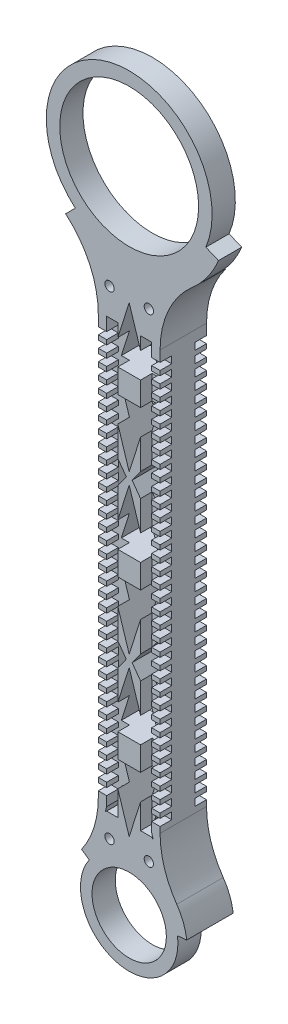
SolidWorks part; units mm, degrees
ref_plane "Front Plane" through (0, 0, 0) normal (0, 0, 1) x (1, 0, 0)
ref_plane "Top Plane" through (0, 0, 0) normal (0, 1, 0) x (1, 0, 0)
ref_plane "Right Plane" through (0, 0, 0) normal (1, 0, 0) x (0, 0, -1)
sketch "Sketch1" plane through (0, 0, 0) normal (0, 0, 1) x (1, 0, 0)
  line L0 (41.9129, -70.1056) -> (48.8352, -72.9599)
  line L1 (-29.4421, -87.2986) -> (-34.7507, -92.6073)
  line L6 (-16.891, -360.115) -> (-16.891, -131.2827)
  line L8 (16.891, -360.115) -> (16.891, -131.2827)
  circle A0 centre (0, -52.8237) radius 37.9584
  arc A1 (41.9129, -70.1056) -> (-29.4421, -87.2986) centre (0, -52.8237) ccw
  arc A2 (-34.7507, -92.6073) -> (-34.5065, -92.8193) centre (0, -52.8237) ccw
  arc A3 (34.5065, -92.8193) -> (48.8352, -72.9599) centre (0, -52.8237) ccw
  arc A4 (16.891, -131.2827) -> (34.5065, -92.8193) centre (67.691, -131.2827) cw
  arc A5 (-16.891, -131.2827) -> (-34.5065, -92.8193) centre (-67.691, -131.2827) ccw
  arc A6 (-26.0165, -389.1645) -> (26.0165, -389.1645) centre (0, -407.2996) ccw
  arc A7 (16.891, -360.115) -> (26.0165, -389.1645) centre (67.691, -360.115) ccw
  arc A8 (-16.891, -360.115) -> (-26.0165, -389.1645) centre (-67.691, -360.115) cw
  point P3 (0, -307.0431)
  dimension "D1" = 50.8
  dimension "D2" = 50.8
extrude "Boss-Extrude1" add sketch "Sketch1" along normal blind 12.7
sketch "Sketch2" plane through (0, 0, 12.7) normal (0, 0, 1) x (1, 0, 0)
  circle A0 centre (0, -407.2996) radius 20.32
  dimension "D1" = 40.64
extrude "Cut-Extrude1" cut sketch "Sketch2" against normal through all
sketch "Sketch3" plane through (0, 0, 12.7) normal (0, 0, 1) x (1, 0, 0)
  line L0 (31.4667, -403.3512) -> (26.4093, -403.8521)
  line L2 (-21.8491, -392.0695) -> (-26.0165, -389.1645)
  arc A2 (-26.0165, -389.1645) -> (26.0165, -389.1645) centre (0, -407.2996) ccw construction
  arc A5 (-26.0165, -389.1645) -> (31.4667, -403.3512) centre (0, -407.2996) ccw
  arc A7 (-21.8491, -392.0695) -> (26.4093, -403.8521) centre (0, -407.2996) ccw
  arc A9 (-21.8491, -392.0695) -> (21.8491, -392.0695) centre (0, -407.2996) ccw construction
  arc A10 (-26.0165, -389.1645) -> (26.0165, -389.1645) centre (0, -407.2996) ccw construction
  arc A11 (16.891, -360.115) -> (26.0165, -389.1645) centre (67.691, -360.115) ccw construction
  arc A12 (11.811, -360.115) -> (21.8491, -392.0695) centre (67.691, -360.115) ccw construction
  arc A13 (-21.8491, -392.0695) -> (-11.811, -360.115) centre (-67.691, -360.115) ccw construction
  arc A14 (-26.0165, -389.1645) -> (-16.891, -360.115) centre (-67.691, -360.115) ccw construction
  dimension "D1" = 5.08
extrude "Cut-Extrude2" cut sketch "Sketch3" against normal through all
sketch "Sketch4" plane through (0, 0, 0) normal (0, 0, -1) x (-1, 0, 0)
  line L0 (-31.4667, -403.3512) -> (-26.4093, -403.8521) construction
  line L1 (21.8491, -392.0695) -> (26.0165, -389.1645) construction
  line L2 (-16.891, -360.115) -> (-16.891, -131.2827) construction
  line L3 (16.891, -131.2827) -> (16.891, -360.115) construction
  line L4 (-31.4667, -403.3512) -> (-27.7291, -403.7214)
  line L5 (22.9366, -391.3114) -> (26.0165, -389.1645)
  line L6 (-16.891, -360.115) -> (-16.891, -131.2827)
  line L7 (16.891, -131.2827) -> (16.891, -360.115)
  arc A0 (-27.4428, -100.2871) -> (27.4428, -100.2871) centre (0, -52.8237) ccw
  arc A1 (22.9366, -391.3114) -> (-27.7291, -403.7214) centre (0, -407.2996) ccw
  arc A2 (-26.0165, -389.1645) -> (-31.4667, -403.3512) centre (0, -407.2996) ccw construction
  arc A3 (-26.0165, -389.1645) -> (-16.891, -360.115) centre (-67.691, -360.115) ccw construction
  arc A4 (16.891, -360.115) -> (26.0165, -389.1645) centre (67.691, -360.115) ccw construction
  arc A5 (-16.891, -131.2827) -> (-34.5065, -92.8193) centre (-67.691, -131.2827) ccw construction
  arc A6 (34.5065, -92.8193) -> (16.891, -131.2827) centre (67.691, -131.2827) ccw construction
  arc A7 (-26.0165, -389.1645) -> (-31.4667, -403.3512) centre (0, -407.2996) ccw
  arc A8 (-26.0165, -389.1645) -> (-16.891, -360.115) centre (-67.691, -360.115) ccw
  arc A9 (16.891, -360.115) -> (26.0165, -389.1645) centre (67.691, -360.115) ccw
  arc A10 (-16.891, -131.2827) -> (-27.4428, -100.2871) centre (-67.691, -131.2827) ccw
  arc A11 (27.4428, -100.2871) -> (16.891, -131.2827) centre (67.691, -131.2827) ccw
extrude "Boss-Extrude2" add sketch "Sketch4" along normal blind 12.7
sketch "Sketch5" plane through (0, 0, -12.7) normal (0, 0, -1) x (-1, 0, 0)
  line L0 (0, -52.8237) -> (0, -407.2996) construction
  line L1 (0, -117.3287) -> (-10.643, -150.8506)
  line L2 (-10.643, -150.8506) -> (10.643, -150.8506)
  line L3 (0, -117.3287) -> (10.643, -150.8506)
  line L4 (-13.7523, -157.3804) -> (13.3679, -157.3804) construction
  line L5 (-10.643, -163.9102) -> (10.643, -163.9102)
  line L6 (0, -197.4321) -> (-10.643, -163.9102)
  line L7 (0, -197.4321) -> (10.643, -163.9102)
  line L8 (0, -203.6887) -> (-10.643, -237.2106)
  line L9 (0, -203.6887) -> (10.643, -237.2106)
  line L10 (-10.643, -237.2106) -> (10.643, -237.2106)
  line L11 (-10.643, -250.2702) -> (10.643, -250.2702)
  line L12 (0, -283.7921) -> (-10.643, -250.2702)
  line L13 (0, -283.7921) -> (10.643, -250.2702)
  line L14 (0, -290.0487) -> (-10.643, -323.5706)
  line L15 (0, -290.0487) -> (10.643, -323.5706)
  line L16 (-10.643, -323.5706) -> (10.643, -323.5706)
  line L17 (-10.643, -336.6302) -> (10.643, -336.6302)
  line L18 (0, -370.1521) -> (-10.643, -336.6302)
  line L19 (0, -370.1521) -> (10.643, -336.6302)
  point P9 (0, -150.8506)
  dimension "D1" = 3
extrude "Cut-Extrude3" cut sketch "Sketch5" against normal through all
sketch "Sketch6" plane through (0, 0, -12.7) normal (0, 0, -1) x (-1, 0, 0)
  line L0 (0, -237.2106) -> (0, -250.2702) construction
  line L1 (-10.643, -237.2106) -> (10.643, -237.2106) construction
  line L2 (10.643, -250.2702) -> (-10.643, -250.2702) construction
  line L3 (0, -243.7404) -> (-16.891, -243.7404) construction
  line L4 (-16.891, -131.2827) -> (-16.891, -360.115) construction
  line L5 (0, -197.4321) -> (0, -203.6887) construction
  line L6 (-1.5941, -200.5506) -> (-16.891, -200.5506) construction
  line L7 (-1.5941, -200.5506) -> (-14.024, -183.3482)
  line L8 (-14.024, -183.3482) -> (-14.024, -217.753)
  line L9 (-1.5941, -200.5506) -> (-14.024, -217.753)
  line L10 (1.5941, -200.5506) -> (14.024, -217.753)
  line L11 (14.024, -183.3482) -> (14.024, -217.753)
  line L12 (1.5941, -200.5506) -> (14.024, -183.3482)
  line L13 (14.024, -304.1326) -> (14.024, -269.7279)
  line L14 (1.5941, -286.9302) -> (14.024, -269.7279)
  line L15 (-1.5941, -286.9302) -> (-14.024, -269.7279)
  line L16 (-14.024, -304.1326) -> (-14.024, -269.7279)
  line L17 (-1.5941, -286.9302) -> (-14.024, -304.1326)
  line L18 (1.5941, -286.9302) -> (14.024, -304.1326)
  line L25 (-10.1561, -354.1919) -> (-7.6855, -361.1596)
  line L26 (-13.0919, -364.9672) -> (-10.1561, -354.1919)
  line L28 (13.0919, -364.9672) -> (10.1561, -354.1919)
  line L29 (10.1561, -354.1919) -> (7.6855, -361.1596)
  arc A0 (13.0919, -364.9672) -> (7.6855, -361.1596) centre (0, -377.8143) ccw
  arc A1 (-7.6855, -361.1596) -> (-13.0919, -364.9672) centre (0, -377.8143) ccw
  point P19 (-14.024, -200.5506)
extrude "Cut-Extrude4" cut sketch "Sketch6" against normal through all
sketch "Sketch7" plane through (0, 0, -12.7) normal (0, 0, -1) x (-1, 0, 0)
  line L0 (-14.9497, -173.4575) -> (-14.9497, -317.6758)
  line L1 (-14.9497, -317.6758) -> (-12.2901, -317.6758)
  line L2 (0, -237.2106) -> (0, -250.2702) construction
  line L3 (-14.9497, -173.4575) -> (-12.2901, -173.4575)
  line L4 (-12.2901, -317.6758) -> (-12.2901, -173.4575)
  line L5 (-14.9497, -245.5666) -> (-12.2901, -173.4575) construction
  line L6 (-14.9497, -245.5666) -> (-12.2901, -317.6758) construction
  line L7 (-10.643, -237.2106) -> (10.643, -237.2106) construction
  line L8 (10.643, -250.2702) -> (-10.643, -250.2702) construction
  line L9 (14.9497, -317.6758) -> (12.2901, -317.6758)
  line L10 (14.9497, -173.4575) -> (12.2901, -173.4575)
  line L11 (14.9497, -173.4575) -> (14.9497, -317.6758)
  line L12 (12.2901, -317.6758) -> (12.2901, -173.4575)
  point P0 (-14.9497, -245.5666)
extrude "Boss-Extrude3" add sketch "Sketch7" against normal up to surface (25.4 mm away) up to face at (-9.8807, -286.9302, 12.7)
sketch "Sketch8" plane through (0, 0, -12.7) normal (0, 0, -1) x (-1, 0, 0)
  line L0 (0, -117.3287) -> (0, -174.7618) construction
  line L1 (16.891, -245.6988) -> (-16.891, -245.6988) construction
  line L2 (16.891, -360.115) -> (16.891, -131.2827) construction
  line L3 (-16.891, -131.2827) -> (-16.891, -360.115) construction
  circle A0 centre (-10.7564, -114.872) radius 2.54
  circle A1 centre (10.7564, -114.872) radius 2.54
  circle A2 centre (-10.7564, -376.5256) radius 2.54
  circle A3 centre (10.7564, -376.5256) radius 2.54
  dimension "D1" = 5.08
extrude "Cut-Extrude5" cut sketch "Sketch8" against normal through all
sketch "Sketch9" plane through (16.891, 0, 0) normal (1, 0, 0) x (0, 0, -1)
  line L0 (12.7, -131.2827) -> (12.7, -360.115) construction
  line L1 (12.7, -353.0709) -> (6.35, -353.0709)
  line L2 (12.7, -346.7209) -> (6.35, -346.7209)
  line L3 (12.7, -356.8809) -> (6.35, -356.8809)
  line L4 (6.35, -353.0709) -> (6.35, -356.8809)
  line L5 (12.7, -354.9759) -> (6.35, -356.8809) construction
  line L6 (12.7, -354.9759) -> (6.35, -353.0709) construction
  line L7 (12.7, -353.0709) -> (12.7, -356.8809)
  line L8 (12.7, -346.7209) -> (12.7, -350.5309)
  line L9 (6.35, -346.7209) -> (6.35, -350.5309)
  line L10 (12.7, -350.5309) -> (6.35, -350.5309)
  line L11 (12.7, -340.3709) -> (6.35, -340.3709)
  line L12 (12.7, -340.3709) -> (12.7, -344.1809)
  line L13 (6.35, -340.3709) -> (6.35, -344.1809)
  line L14 (12.7, -344.1809) -> (6.35, -344.1809)
  line L15 (12.7, -334.0209) -> (6.35, -334.0209)
  line L16 (12.7, -334.0209) -> (12.7, -337.8309)
  line L17 (6.35, -334.0209) -> (6.35, -337.8309)
  line L18 (12.7, -337.8309) -> (6.35, -337.8309)
  line L19 (12.7, -327.6709) -> (6.35, -327.6709)
  line L20 (12.7, -327.6709) -> (12.7, -331.4809)
  line L21 (6.35, -327.6709) -> (6.35, -331.4809)
  line L22 (12.7, -331.4809) -> (6.35, -331.4809)
  line L23 (12.7, -321.3209) -> (6.35, -321.3209)
  line L24 (12.7, -321.3209) -> (12.7, -325.1309)
  line L25 (6.35, -321.3209) -> (6.35, -325.1309)
  line L26 (12.7, -325.1309) -> (6.35, -325.1309)
  line L27 (12.7, -314.9709) -> (6.35, -314.9709)
  line L28 (12.7, -314.9709) -> (12.7, -318.7809)
  line L29 (6.35, -314.9709) -> (6.35, -318.7809)
  line L30 (12.7, -318.7809) -> (6.35, -318.7809)
  line L31 (12.7, -308.6209) -> (6.35, -308.6209)
  line L32 (12.7, -308.6209) -> (12.7, -312.4309)
  line L33 (6.35, -308.6209) -> (6.35, -312.4309)
  line L34 (12.7, -312.4309) -> (6.35, -312.4309)
  line L35 (12.7, -302.2709) -> (6.35, -302.2709)
  line L36 (12.7, -302.2709) -> (12.7, -306.0809)
  line L37 (6.35, -302.2709) -> (6.35, -306.0809)
  line L38 (12.7, -306.0809) -> (6.35, -306.0809)
  line L39 (12.7, -295.9209) -> (6.35, -295.9209)
  line L40 (12.7, -295.9209) -> (12.7, -299.7309)
  line L41 (6.35, -295.9209) -> (6.35, -299.7309)
  line L42 (12.7, -299.7309) -> (6.35, -299.7309)
  line L43 (12.7, -289.5709) -> (6.35, -289.5709)
  line L44 (12.7, -289.5709) -> (12.7, -293.3809)
  line L45 (6.35, -289.5709) -> (6.35, -293.3809)
  line L46 (12.7, -293.3809) -> (6.35, -293.3809)
  line L47 (12.7, -283.2209) -> (6.35, -283.2209)
  line L48 (12.7, -283.2209) -> (12.7, -287.0309)
  line L49 (6.35, -283.2209) -> (6.35, -287.0309)
  line L50 (12.7, -287.0309) -> (6.35, -287.0309)
  line L51 (12.7, -276.8709) -> (6.35, -276.8709)
  line L52 (12.7, -276.8709) -> (12.7, -280.6809)
  line L53 (6.35, -276.8709) -> (6.35, -280.6809)
  line L54 (12.7, -280.6809) -> (6.35, -280.6809)
  line L55 (12.7, -270.5209) -> (6.35, -270.5209)
  line L56 (12.7, -270.5209) -> (12.7, -274.3309)
  line L57 (6.35, -270.5209) -> (6.35, -274.3309)
  line L58 (12.7, -274.3309) -> (6.35, -274.3309)
  line L59 (12.7, -264.1709) -> (6.35, -264.1709)
  line L60 (12.7, -264.1709) -> (12.7, -267.9809)
  line L61 (6.35, -264.1709) -> (6.35, -267.9809)
  line L62 (12.7, -267.9809) -> (6.35, -267.9809)
  line L63 (12.7, -257.8209) -> (6.35, -257.8209)
  line L64 (12.7, -257.8209) -> (12.7, -261.6309)
  line L65 (6.35, -257.8209) -> (6.35, -261.6309)
  line L66 (12.7, -261.6309) -> (6.35, -261.6309)
  line L67 (12.7, -251.4709) -> (6.35, -251.4709)
  line L68 (12.7, -251.4709) -> (12.7, -255.2809)
  line L69 (6.35, -251.4709) -> (6.35, -255.2809)
  line L70 (12.7, -255.2809) -> (6.35, -255.2809)
  line L71 (12.7, -245.1209) -> (6.35, -245.1209)
  line L72 (12.7, -245.1209) -> (12.7, -248.9309)
  line L73 (6.35, -245.1209) -> (6.35, -248.9309)
  line L74 (12.7, -248.9309) -> (6.35, -248.9309)
  line L75 (12.7, -238.7709) -> (6.35, -238.7709)
  line L76 (12.7, -238.7709) -> (12.7, -242.5809)
  line L77 (6.35, -238.7709) -> (6.35, -242.5809)
  line L78 (12.7, -242.5809) -> (6.35, -242.5809)
  line L79 (12.7, -232.4209) -> (6.35, -232.4209)
  line L80 (12.7, -232.4209) -> (12.7, -236.2309)
  line L81 (6.35, -232.4209) -> (6.35, -236.2309)
  line L82 (12.7, -236.2309) -> (6.35, -236.2309)
  line L83 (12.7, -226.0709) -> (6.35, -226.0709)
  line L84 (12.7, -226.0709) -> (12.7, -229.8809)
  line L85 (6.35, -226.0709) -> (6.35, -229.8809)
  line L86 (12.7, -229.8809) -> (6.35, -229.8809)
  line L87 (12.7, -219.7209) -> (6.35, -219.7209)
  line L88 (12.7, -219.7209) -> (12.7, -223.5309)
  line L89 (6.35, -219.7209) -> (6.35, -223.5309)
  line L90 (12.7, -223.5309) -> (6.35, -223.5309)
  line L91 (12.7, -213.3709) -> (6.35, -213.3709)
  line L92 (12.7, -213.3709) -> (12.7, -217.1809)
  line L93 (6.35, -213.3709) -> (6.35, -217.1809)
  line L94 (12.7, -217.1809) -> (6.35, -217.1809)
  line L95 (12.7, -207.0209) -> (6.35, -207.0209)
  line L96 (12.7, -207.0209) -> (12.7, -210.8309)
  line L97 (6.35, -207.0209) -> (6.35, -210.8309)
  line L98 (12.7, -210.8309) -> (6.35, -210.8309)
  line L99 (12.7, -200.6709) -> (6.35, -200.6709)
  line L100 (12.7, -200.6709) -> (12.7, -204.4809)
  line L101 (6.35, -200.6709) -> (6.35, -204.4809)
  line L102 (12.7, -204.4809) -> (6.35, -204.4809)
  line L103 (12.7, -194.3209) -> (6.35, -194.3209)
  line L104 (12.7, -194.3209) -> (12.7, -198.1309)
  line L105 (6.35, -194.3209) -> (6.35, -198.1309)
  line L106 (12.7, -198.1309) -> (6.35, -198.1309)
  line L107 (12.7, -187.9709) -> (6.35, -187.9709)
  line L108 (12.7, -187.9709) -> (12.7, -191.7809)
  line L109 (6.35, -187.9709) -> (6.35, -191.7809)
  line L110 (12.7, -191.7809) -> (6.35, -191.7809)
  line L111 (12.7, -181.6209) -> (6.35, -181.6209)
  line L112 (12.7, -181.6209) -> (12.7, -185.4309)
  line L113 (6.35, -181.6209) -> (6.35, -185.4309)
  line L114 (12.7, -185.4309) -> (6.35, -185.4309)
  line L115 (12.7, -175.2709) -> (6.35, -175.2709)
  line L116 (12.7, -175.2709) -> (12.7, -179.0809)
  line L117 (6.35, -175.2709) -> (6.35, -179.0809)
  line L118 (12.7, -179.0809) -> (6.35, -179.0809)
  line L119 (12.7, -168.9209) -> (6.35, -168.9209)
  line L120 (12.7, -168.9209) -> (12.7, -172.7309)
  line L121 (6.35, -168.9209) -> (6.35, -172.7309)
  line L122 (12.7, -172.7309) -> (6.35, -172.7309)
  line L123 (12.7, -162.5709) -> (6.35, -162.5709)
  line L124 (12.7, -162.5709) -> (12.7, -166.3809)
  line L125 (6.35, -162.5709) -> (6.35, -166.3809)
  line L126 (12.7, -166.3809) -> (6.35, -166.3809)
  line L127 (12.7, -156.2209) -> (6.35, -156.2209)
  line L128 (12.7, -156.2209) -> (12.7, -160.0309)
  line L129 (6.35, -156.2209) -> (6.35, -160.0309)
  line L130 (12.7, -160.0309) -> (6.35, -160.0309)
  line L131 (12.7, -149.8709) -> (6.35, -149.8709)
  line L132 (12.7, -149.8709) -> (12.7, -153.6809)
  line L133 (6.35, -149.8709) -> (6.35, -153.6809)
  line L134 (12.7, -153.6809) -> (6.35, -153.6809)
  line L135 (12.7, -143.5209) -> (6.35, -143.5209)
  line L136 (12.7, -143.5209) -> (12.7, -147.3309)
  line L137 (6.35, -143.5209) -> (6.35, -147.3309)
  line L138 (12.7, -147.3309) -> (6.35, -147.3309)
  line L139 (12.7, -137.1709) -> (6.35, -137.1709)
  line L140 (12.7, -137.1709) -> (12.7, -140.9809)
  line L141 (6.35, -137.1709) -> (6.35, -140.9809)
  line L142 (12.7, -140.9809) -> (6.35, -140.9809)
  line L143 (0, -131.2827) -> (0, -360.115) construction
  line L144 (-12.7, -131.2827) -> (12.7, -131.2827) construction
  line L145 (-12.7, -360.115) -> (12.7, -360.115) construction
  line L146 (-12.7, -354.9759) -> (-6.35, -353.0709) construction
  line L147 (-12.7, -354.9759) -> (-6.35, -356.8809) construction
  line L148 (-12.7, -140.9809) -> (-6.35, -140.9809)
  line L149 (-6.35, -137.1709) -> (-6.35, -140.9809)
  line L150 (-12.7, -137.1709) -> (-12.7, -140.9809)
  line L151 (-12.7, -137.1709) -> (-6.35, -137.1709)
  line L152 (-12.7, -147.3309) -> (-6.35, -147.3309)
  line L153 (-6.35, -143.5209) -> (-6.35, -147.3309)
  line L154 (-12.7, -143.5209) -> (-12.7, -147.3309)
  line L155 (-12.7, -143.5209) -> (-6.35, -143.5209)
  line L156 (-12.7, -153.6809) -> (-6.35, -153.6809)
  line L157 (-6.35, -149.8709) -> (-6.35, -153.6809)
  line L158 (-12.7, -149.8709) -> (-12.7, -153.6809)
  line L159 (-12.7, -149.8709) -> (-6.35, -149.8709)
  line L160 (-12.7, -160.0309) -> (-6.35, -160.0309)
  line L161 (-6.35, -156.2209) -> (-6.35, -160.0309)
  line L162 (-12.7, -156.2209) -> (-12.7, -160.0309)
  line L163 (-12.7, -156.2209) -> (-6.35, -156.2209)
  line L164 (-12.7, -166.3809) -> (-6.35, -166.3809)
  line L165 (-6.35, -162.5709) -> (-6.35, -166.3809)
  line L166 (-12.7, -162.5709) -> (-12.7, -166.3809)
  line L167 (-12.7, -162.5709) -> (-6.35, -162.5709)
  line L168 (-12.7, -172.7309) -> (-6.35, -172.7309)
  line L169 (-6.35, -168.9209) -> (-6.35, -172.7309)
  line L170 (-12.7, -168.9209) -> (-12.7, -172.7309)
  line L171 (-12.7, -168.9209) -> (-6.35, -168.9209)
  line L172 (-12.7, -179.0809) -> (-6.35, -179.0809)
  line L173 (-6.35, -175.2709) -> (-6.35, -179.0809)
  line L174 (-12.7, -175.2709) -> (-12.7, -179.0809)
  line L175 (-12.7, -175.2709) -> (-6.35, -175.2709)
  line L176 (-12.7, -185.4309) -> (-6.35, -185.4309)
  line L177 (-6.35, -181.6209) -> (-6.35, -185.4309)
  line L178 (-12.7, -181.6209) -> (-12.7, -185.4309)
  line L179 (-12.7, -181.6209) -> (-6.35, -181.6209)
  line L180 (-12.7, -191.7809) -> (-6.35, -191.7809)
  line L181 (-6.35, -187.9709) -> (-6.35, -191.7809)
  line L182 (-12.7, -187.9709) -> (-12.7, -191.7809)
  line L183 (-12.7, -187.9709) -> (-6.35, -187.9709)
  line L184 (-12.7, -198.1309) -> (-6.35, -198.1309)
  line L185 (-6.35, -194.3209) -> (-6.35, -198.1309)
  line L186 (-12.7, -194.3209) -> (-12.7, -198.1309)
  line L187 (-12.7, -194.3209) -> (-6.35, -194.3209)
  line L188 (-12.7, -204.4809) -> (-6.35, -204.4809)
  line L189 (-6.35, -200.6709) -> (-6.35, -204.4809)
  line L190 (-12.7, -200.6709) -> (-12.7, -204.4809)
  line L191 (-12.7, -200.6709) -> (-6.35, -200.6709)
  line L192 (-12.7, -210.8309) -> (-6.35, -210.8309)
  line L193 (-6.35, -207.0209) -> (-6.35, -210.8309)
  line L194 (-12.7, -207.0209) -> (-12.7, -210.8309)
  line L195 (-12.7, -207.0209) -> (-6.35, -207.0209)
  line L196 (-12.7, -217.1809) -> (-6.35, -217.1809)
  line L197 (-6.35, -213.3709) -> (-6.35, -217.1809)
  line L198 (-12.7, -213.3709) -> (-12.7, -217.1809)
  line L199 (-12.7, -213.3709) -> (-6.35, -213.3709)
  line L200 (-12.7, -223.5309) -> (-6.35, -223.5309)
  line L201 (-6.35, -219.7209) -> (-6.35, -223.5309)
  line L202 (-12.7, -219.7209) -> (-12.7, -223.5309)
  line L203 (-12.7, -219.7209) -> (-6.35, -219.7209)
  line L204 (-12.7, -229.8809) -> (-6.35, -229.8809)
  line L205 (-6.35, -226.0709) -> (-6.35, -229.8809)
  line L206 (-12.7, -226.0709) -> (-12.7, -229.8809)
  line L207 (-12.7, -226.0709) -> (-6.35, -226.0709)
  line L208 (-12.7, -236.2309) -> (-6.35, -236.2309)
  line L209 (-6.35, -232.4209) -> (-6.35, -236.2309)
  line L210 (-12.7, -232.4209) -> (-12.7, -236.2309)
  line L211 (-12.7, -232.4209) -> (-6.35, -232.4209)
  line L212 (-12.7, -242.5809) -> (-6.35, -242.5809)
  line L213 (-6.35, -238.7709) -> (-6.35, -242.5809)
  line L214 (-12.7, -238.7709) -> (-12.7, -242.5809)
  line L215 (-12.7, -238.7709) -> (-6.35, -238.7709)
  line L216 (-12.7, -248.9309) -> (-6.35, -248.9309)
  line L217 (-6.35, -245.1209) -> (-6.35, -248.9309)
  line L218 (-12.7, -245.1209) -> (-12.7, -248.9309)
  line L219 (-12.7, -245.1209) -> (-6.35, -245.1209)
  line L220 (-12.7, -255.2809) -> (-6.35, -255.2809)
  line L221 (-6.35, -251.4709) -> (-6.35, -255.2809)
  line L222 (-12.7, -251.4709) -> (-12.7, -255.2809)
  line L223 (-12.7, -251.4709) -> (-6.35, -251.4709)
  line L224 (-12.7, -261.6309) -> (-6.35, -261.6309)
  line L225 (-6.35, -257.8209) -> (-6.35, -261.6309)
  line L226 (-12.7, -257.8209) -> (-12.7, -261.6309)
  line L227 (-12.7, -257.8209) -> (-6.35, -257.8209)
  line L228 (-12.7, -267.9809) -> (-6.35, -267.9809)
  line L229 (-6.35, -264.1709) -> (-6.35, -267.9809)
  line L230 (-12.7, -264.1709) -> (-12.7, -267.9809)
  line L231 (-12.7, -264.1709) -> (-6.35, -264.1709)
  line L232 (-12.7, -274.3309) -> (-6.35, -274.3309)
  line L233 (-6.35, -270.5209) -> (-6.35, -274.3309)
  line L234 (-12.7, -270.5209) -> (-12.7, -274.3309)
  line L235 (-12.7, -270.5209) -> (-6.35, -270.5209)
  line L236 (-12.7, -280.6809) -> (-6.35, -280.6809)
  line L237 (-6.35, -276.8709) -> (-6.35, -280.6809)
  line L238 (-12.7, -276.8709) -> (-12.7, -280.6809)
  line L239 (-12.7, -276.8709) -> (-6.35, -276.8709)
  line L240 (-12.7, -287.0309) -> (-6.35, -287.0309)
  line L241 (-6.35, -283.2209) -> (-6.35, -287.0309)
  line L242 (-12.7, -283.2209) -> (-12.7, -287.0309)
  line L243 (-12.7, -283.2209) -> (-6.35, -283.2209)
  line L244 (-12.7, -293.3809) -> (-6.35, -293.3809)
  line L245 (-6.35, -289.5709) -> (-6.35, -293.3809)
  line L246 (-12.7, -289.5709) -> (-12.7, -293.3809)
  line L247 (-12.7, -289.5709) -> (-6.35, -289.5709)
  line L248 (-12.7, -299.7309) -> (-6.35, -299.7309)
  line L249 (-6.35, -295.9209) -> (-6.35, -299.7309)
  line L250 (-12.7, -295.9209) -> (-12.7, -299.7309)
  line L251 (-12.7, -295.9209) -> (-6.35, -295.9209)
  line L252 (-12.7, -306.0809) -> (-6.35, -306.0809)
  line L253 (-6.35, -302.2709) -> (-6.35, -306.0809)
  line L254 (-12.7, -302.2709) -> (-12.7, -306.0809)
  line L255 (-12.7, -302.2709) -> (-6.35, -302.2709)
  line L256 (-12.7, -312.4309) -> (-6.35, -312.4309)
  line L257 (-6.35, -308.6209) -> (-6.35, -312.4309)
  line L258 (-12.7, -308.6209) -> (-12.7, -312.4309)
  line L259 (-12.7, -308.6209) -> (-6.35, -308.6209)
  line L260 (-12.7, -318.7809) -> (-6.35, -318.7809)
  line L261 (-6.35, -314.9709) -> (-6.35, -318.7809)
  line L262 (-12.7, -314.9709) -> (-12.7, -318.7809)
  line L263 (-12.7, -314.9709) -> (-6.35, -314.9709)
  line L264 (-12.7, -325.1309) -> (-6.35, -325.1309)
  line L265 (-6.35, -321.3209) -> (-6.35, -325.1309)
  line L266 (-12.7, -321.3209) -> (-12.7, -325.1309)
  line L267 (-12.7, -321.3209) -> (-6.35, -321.3209)
  line L268 (-12.7, -331.4809) -> (-6.35, -331.4809)
  line L269 (-6.35, -327.6709) -> (-6.35, -331.4809)
  line L270 (-12.7, -327.6709) -> (-12.7, -331.4809)
  line L271 (-12.7, -327.6709) -> (-6.35, -327.6709)
  line L272 (-12.7, -337.8309) -> (-6.35, -337.8309)
  line L273 (-6.35, -334.0209) -> (-6.35, -337.8309)
  line L274 (-12.7, -334.0209) -> (-12.7, -337.8309)
  line L275 (-12.7, -334.0209) -> (-6.35, -334.0209)
  line L276 (-12.7, -344.1809) -> (-6.35, -344.1809)
  line L277 (-6.35, -340.3709) -> (-6.35, -344.1809)
  line L278 (-12.7, -340.3709) -> (-12.7, -344.1809)
  line L279 (-12.7, -340.3709) -> (-6.35, -340.3709)
  line L280 (-12.7, -350.5309) -> (-6.35, -350.5309)
  line L281 (-6.35, -346.7209) -> (-6.35, -350.5309)
  line L282 (-12.7, -346.7209) -> (-12.7, -350.5309)
  line L283 (-12.7, -353.0709) -> (-12.7, -356.8809)
  line L284 (-6.35, -353.0709) -> (-6.35, -356.8809)
  line L285 (-12.7, -356.8809) -> (-6.35, -356.8809)
  line L286 (-12.7, -346.7209) -> (-6.35, -346.7209)
  line L287 (-12.7, -353.0709) -> (-6.35, -353.0709)
  point P0 (12.7, -354.9759)
  dimension "D1" = 35
extrude "Cut-Extrude6" cut sketch "Sketch9" against normal blind 6.35
sketch "Sketch10" plane through (0, 0, -12.7) normal (0, 0, -1) x (-1, 0, 0)
  line L0 (16.891, -245.6988) -> (-7.6126, -245.6988) construction
  line L1 (16.891, -360.115) -> (16.891, -131.2827) construction
  line L2 (-12.3039, -129.8722) -> (-6.2149, -129.8722)
  line L3 (-6.2149, -364.2055) -> (-12.3039, -364.2055)
  line L6 (-12.3039, -364.2055) -> (-12.3039, -129.8722)
  line L7 (-6.2149, -302.2612) -> (-10.4748, -129.8722) construction
  line L8 (-6.2149, -210.3919) -> (-12.3039, -364.2055) construction
  line L9 (-6.2149, -129.8722) -> (-6.2149, -364.2055)
extrude "Cut-Extrude8" cut sketch "Sketch10" against normal blind 6.35
mirror "Mirror1" about plane through (0, 0, 0) normal (0, 0, 1) of "Cut-Extrude8"
mirror "Mirror2" about plane through (0, 0, 0) normal (1, 0, 0) of "Mirror1", "Cut-Extrude8"
mirror "Mirror3" about plane through (0, 0, 0) normal (1, 0, 0) of "Cut-Extrude6"
